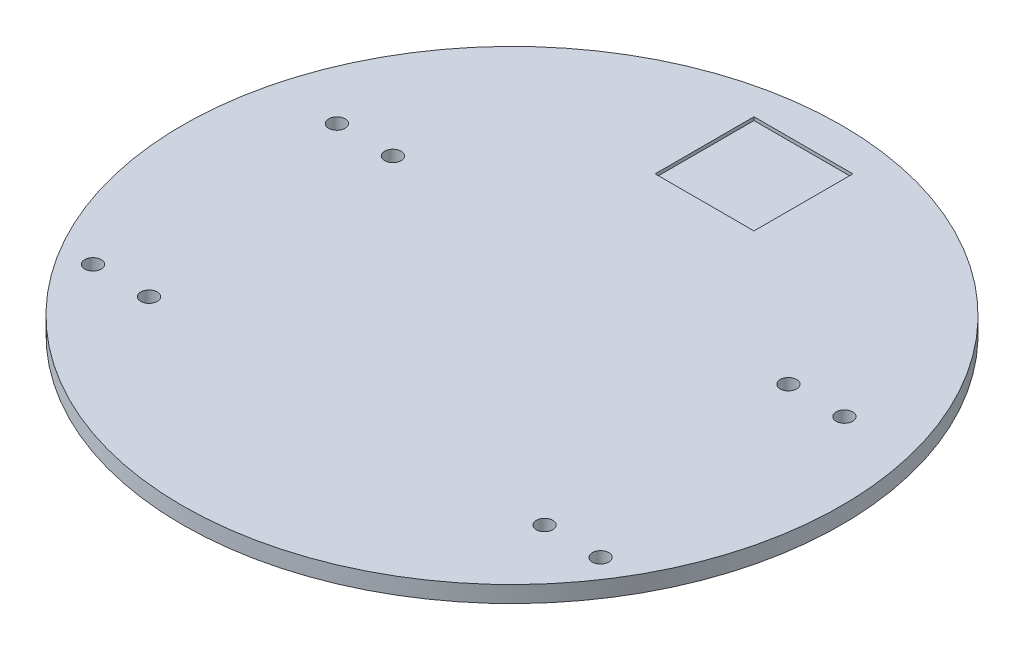
SolidWorks part; units mm, degrees
ref_plane "Front Plane" through (0, 0, 0) normal (0, 0, 1) x (1, 0, 0)
ref_plane "Top Plane" through (0, 0, 0) normal (0, 1, 0) x (1, 0, 0)
ref_plane "Right Plane" through (0, 0, 0) normal (1, 0, 0) x (0, 0, -1)
sketch "Sketch1" plane through (0, 0, 0) normal (0, 1, 0) x (1, 0, 0)
  circle A0 centre (0, 0) radius 100
  dimension "D1" = 200
extrude "Boss-Extrude1" add sketch "Sketch1" along normal blind 5
sketch "Sketch2" plane through (0, 5, 0) normal (0, 1, 0) x (1, 0, 0)
  line L0 (-100, 0) -> (100, 0) construction
  line L1 (-77, -50.1283) -> (-77, 23.8717) construction
  line L2 (0, -100) -> (0, 100) construction
  line L3 (-74.5, 23.8717) -> (-62.5, 23.8717) construction
  line L4 (-60, 23.8717) -> (-60, -50.1283) construction
  line L5 (-77, -50.1283) -> (-60, -50.1283) construction
  line L6 (77, -50.1283) -> (60, -50.1283) construction
  line L7 (60, 23.8717) -> (60, -50.1283) construction
  line L8 (77, 23.8717) -> (60, 23.8717) construction
  line L9 (77, -50.1283) -> (77, 23.8717) construction
  circle A0 centre (0, 0) radius 100 construction
  circle A1 centre (-77, -50.1283) radius 2.5
  circle A2 centre (-77, 23.8717) radius 2.5
  circle A3 centre (-60, -50.1283) radius 2.5
  circle A4 centre (-60, 23.8717) radius 2.5
  circle A5 centre (60, 23.8717) radius 2.5
  circle A6 centre (60, -50.1283) radius 2.5
  circle A7 centre (77, 23.8717) radius 2.5
  circle A8 centre (77, -50.1283) radius 2.5
  dimension "D1" = 12
  dimension "D3" = 5
  dimension "D4" = 60
  dimension "D2" = 74
extrude "Cut-Extrude1" cut sketch "Sketch2" against normal blind 10
sketch "Sketch3" plane through (0, 5, 0) normal (0, 1, 0) x (1, 0, 0)
  line L6 (-100, 0) -> (100, 0) construction
  line L7 (-80.787, 58.9361) -> (80.787, 58.9361) construction
  line L8 (-15.5083, 58.9361) -> (14.4917, 58.9361)
  line L9 (-15.5083, 88.9361) -> (14.4917, 88.9361)
  line L10 (14.4917, 58.9361) -> (14.4917, 88.9361)
  line L11 (-15.5083, 58.9361) -> (-15.5083, 88.9361)
  circle A0 centre (0, 0) radius 100 construction
extrude "Cut-Extrude2" cut sketch "Sketch3" against normal blind 1
